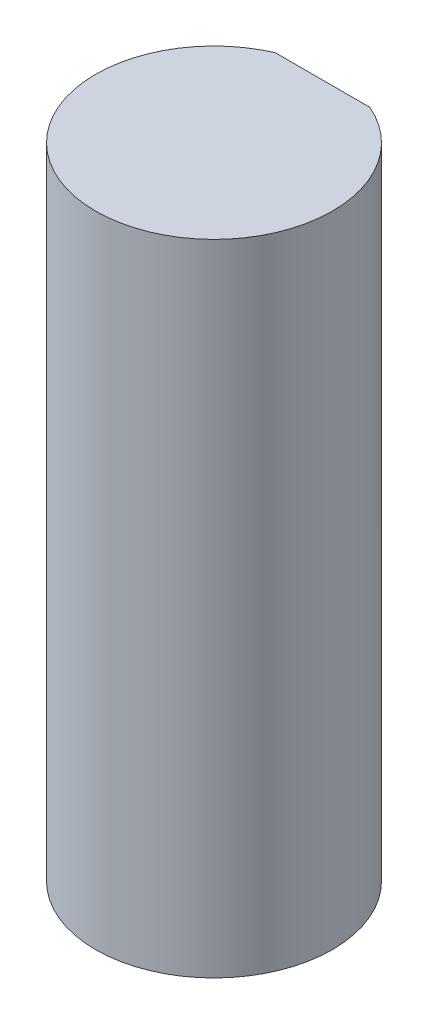
SolidWorks part; units mm, degrees
ref_plane "Front Plane" through (0, 0, 0) normal (0, 0, 1) x (1, 0, 0)
ref_plane "Top Plane" through (0, 0, 0) normal (0, 1, 0) x (1, 0, 0)
ref_plane "Right Plane" through (0, 0, 0) normal (1, 0, 0) x (0, 0, -1)
sketch "Sketch3" plane through (0, 0, 0) normal (0, 1, 0) x (1, 0, 0)
  circle A0 centre (0, 0) radius 3
  dimension "D1" = 6
extrude "Boss-Extrude2" add sketch "Sketch3" along normal blind 16.2
ref_plane "Plane1" through (0, 16.2, 0) normal (0, 1, 0) x (1, 0, 0)
sketch "Sketch4" plane through (0, 16.2, 0) normal (0, 1, 0) x (1, 0, 0)
  line L1 (-1.199, 2.75) -> (1.199, 2.75)
  arc A0 (1.199, 2.75) -> (-1.199, 2.75) centre (0, 0) ccw
  point P7 (0, 2.75)
extrude "Cut-Extrude1" cut sketch "Sketch4" against normal blind 12
